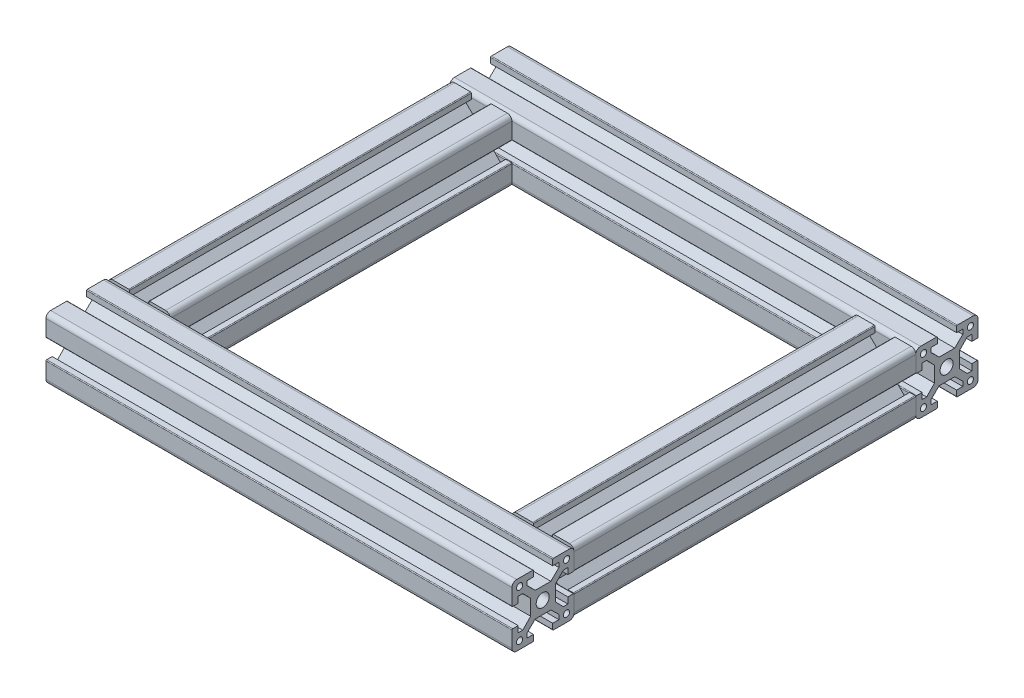
SolidWorks part; units mm, degrees
ref_plane "Front Plane" through (0, 0, 0) normal (0, 0, 1) x (1, 0, 0)
ref_plane "Top Plane" through (0, 0, 0) normal (0, 1, 0) x (1, 0, 0)
ref_plane "Right Plane" through (0, 0, 0) normal (1, 0, 0) x (0, 0, -1)
sketch "Sketch1" plane through (0, 0, 0) normal (0, 1, 0) x (1, 0, 0)
  line L0 (83.72, -89.3533) -> (-46.28, 40.6467) construction
  line L1 (-46.28, 40.6467) -> (83.72, 40.6467)
  line L2 (-46.28, 40.6467) -> (-46.28, -89.3533)
  line L3 (-46.28, -89.3533) -> (83.72, -89.3533)
  line L4 (83.72, 40.6467) -> (83.72, -89.3533)
  line L5 (-46.28, -89.3533) -> (83.72, 40.6467) construction
  dimension "D1" = 130
  dimension "D2" = 130
other "Xa XA-2020T(1)"
ref_plane "Plane1" through (-46.28, 0, -40.6467) normal (1, 0, 0) x (0, 0, -1)
sketch "Sketch11" plane through (-46.28, 0, -40.6467) normal (1, 0, 0) x (0, 0, -1)
  line L0 (-9.8891, 9.9394) -> (10.1109, -10.0606) construction
  line L1 (-9.8891, 9.9394) -> (10.1109, 9.9394) construction
  line L2 (-9.8891, 9.9394) -> (-9.8891, -10.0606) construction
  line L3 (-9.8891, -10.0606) -> (10.1109, -10.0606) construction
  line L4 (10.1109, 9.9394) -> (10.1109, -10.0606) construction
  line L5 (-9.8891, -10.0606) -> (10.1109, 9.9394) construction
  line L6 (0.1109, 9.9394) -> (0.1109, -10.0606) construction
  line L7 (10.1109, -0.0606) -> (-9.8891, -0.0606) construction
  line L88 (-9.8891, 8.4394) -> (-9.8891, 3.2894)
  line L89 (-9.6391, 3.0394) -> (-7.8891, 3.0394)
  line L90 (-7.8891, 3.0394) -> (-7.8891, 5.0394)
  line L91 (-7.8891, 5.0394) -> (-6.4169, 5.0394)
  line L92 (-6.4169, 5.0394) -> (-3.8891, 2.4394)
  line L93 (-3.8891, 2.4394) -> (-3.8891, -2.5606)
  line L94 (-3.8891, -2.5606) -> (-6.4169, -5.1606)
  line L95 (-6.4169, -5.1606) -> (-7.8891, -5.1606)
  line L96 (-7.8891, -5.1606) -> (-7.8891, -3.1606)
  line L97 (-7.8891, -3.1606) -> (-9.6391, -3.1606)
  line L98 (-9.8891, -3.4106) -> (-9.8891, -8.5606)
  line L99 (-8.3891, -10.0606) -> (-3.2391, -10.0606)
  line L100 (-2.9891, -9.8106) -> (-2.9891, -8.0606)
  line L101 (-2.9891, -8.0606) -> (-4.9891, -8.0606)
  line L102 (-4.9891, -8.0606) -> (-4.9891, -6.5883)
  line L103 (-4.9891, -6.5883) -> (-2.3891, -4.0606)
  line L104 (-2.3891, -4.0606) -> (2.6109, -4.0606)
  line L105 (2.6109, -4.0606) -> (5.2109, -6.5883)
  line L106 (5.2109, -6.5883) -> (5.2109, -8.0606)
  line L107 (5.2109, -8.0606) -> (3.2109, -8.0606)
  line L108 (3.2109, -8.0606) -> (3.2109, -9.8106)
  line L109 (3.4609, -10.0606) -> (8.6109, -10.0606)
  line L110 (10.1109, -8.5606) -> (10.1109, -3.4106)
  line L111 (9.8609, -3.1606) -> (8.1109, -3.1606)
  line L112 (8.1109, -3.1606) -> (8.1109, -5.1606)
  line L113 (8.1109, -5.1606) -> (6.6387, -5.1606)
  line L114 (6.6387, -5.1606) -> (4.1109, -2.5606)
  line L115 (4.1109, -2.5606) -> (4.1109, 2.4394)
  line L116 (4.1109, 2.4394) -> (6.6387, 5.0394)
  line L117 (6.6387, 5.0394) -> (8.1109, 5.0394)
  line L118 (8.1109, 5.0394) -> (8.1109, 3.0394)
  line L119 (8.1109, 3.0394) -> (9.8609, 3.0394)
  line L120 (10.1109, 3.2894) -> (10.1109, 8.4394)
  line L121 (8.6109, 9.9394) -> (3.4609, 9.9394)
  line L122 (3.2109, 9.6894) -> (3.2109, 7.9394)
  line L123 (3.2109, 7.9394) -> (5.2109, 7.9394)
  line L124 (5.2109, 7.9394) -> (5.2109, 6.4672)
  line L125 (5.2109, 6.4672) -> (2.6109, 3.9394)
  line L126 (2.6109, 3.9394) -> (-2.3891, 3.9394)
  line L127 (-2.3891, 3.9394) -> (-4.9891, 6.4672)
  line L128 (-4.9891, 6.4672) -> (-4.9891, 7.9394)
  line L129 (-4.9891, 7.9394) -> (-2.9891, 7.9394)
  line L130 (-2.9891, 7.9394) -> (-2.9891, 9.6894)
  line L131 (-3.2391, 9.9394) -> (-8.3891, 9.9394)
  circle A0 centre (-7.4391, 7.4894) radius 1
  circle A1 centre (7.6609, 7.4894) radius 1
  circle A2 centre (-7.4391, -7.6106) radius 1
  circle A3 centre (7.6609, -7.6106) radius 1
  circle A4 centre (0, 0) radius 2.1
  arc A26 (-9.8891, 3.2894) -> (-9.6391, 3.0394) centre (-9.6391, 3.2894) ccw
  arc A27 (-9.6391, -3.1606) -> (-9.8891, -3.4106) centre (-9.6391, -3.4106) ccw
  arc A28 (-9.8891, -8.5606) -> (-8.3891, -10.0606) centre (-8.3891, -8.5606) ccw
  arc A29 (-3.2391, -10.0606) -> (-2.9891, -9.8106) centre (-3.2391, -9.8106) ccw
  arc A30 (3.2109, -9.8106) -> (3.4609, -10.0606) centre (3.4609, -9.8106) ccw
  arc A31 (8.6109, -10.0606) -> (10.1109, -8.5606) centre (8.6109, -8.5606) ccw
  arc A32 (10.1109, -3.4106) -> (9.8609, -3.1606) centre (9.8609, -3.4106) ccw
  arc A33 (9.8609, 3.0394) -> (10.1109, 3.2894) centre (9.8609, 3.2894) ccw
  arc A34 (10.1109, 8.4394) -> (8.6109, 9.9394) centre (8.6109, 8.4394) ccw
  arc A35 (3.4609, 9.9394) -> (3.2109, 9.6894) centre (3.4609, 9.6894) ccw
  arc A36 (-2.9891, 9.6894) -> (-3.2391, 9.9394) centre (-3.2391, 9.6894) ccw
  arc A37 (-8.3891, 9.9394) -> (-9.8891, 8.4394) centre (-8.3891, 8.4394) ccw
  point P52 (0, 0)
